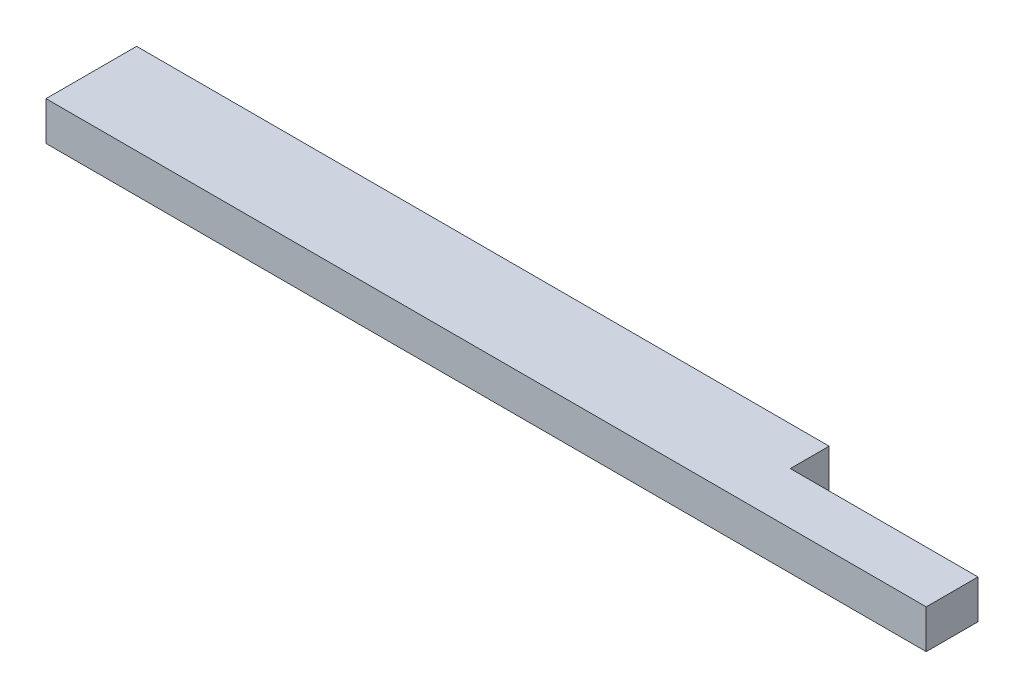
SolidWorks part; units mm, degrees
material "Pine"
ref_plane "Front Plane" through (0, 0, 0) normal (0, 0, 1) x (1, 0, 0)
ref_plane "Top Plane" through (0, 0, 0) normal (0, 1, 0) x (1, 0, 0)
ref_plane "Right Plane" through (0, 0, 0) normal (1, 0, 0) x (0, 0, -1)
sketch "Sketch1" plane through (0, 0, 0) normal (0, 1, 0) x (1, 0, 0)
  line L1 (0, 0) -> (863.6, 0)
  line L2 (0, 0) -> (0, 88.9)
  line L3 (0, 88.9) -> (863.6, 88.9)
  line L4 (863.6, 0) -> (863.6, 88.9)
  dimension "D1" = 88.9
  dimension "D2" = 863.6
extrude "Boss-Extrude1" add sketch "Sketch1" along normal blind 38.1
sketch "Sketch3" plane through (0, 38.1, 0) normal (0, 1, 0) x (1, 0, 0)
  line L5 (863.6, 88.9) -> (679.45, 88.9)
  line L6 (863.6, 88.9) -> (863.6, 50.8)
  line L7 (863.6, 50.8) -> (679.45, 50.8)
  line L8 (679.45, 88.9) -> (679.45, 50.8)
  dimension "D2" = 184.15
  dimension "D4" = 38.1
extrude "Cut-Extrude1" cut sketch "Sketch3" against normal through all
